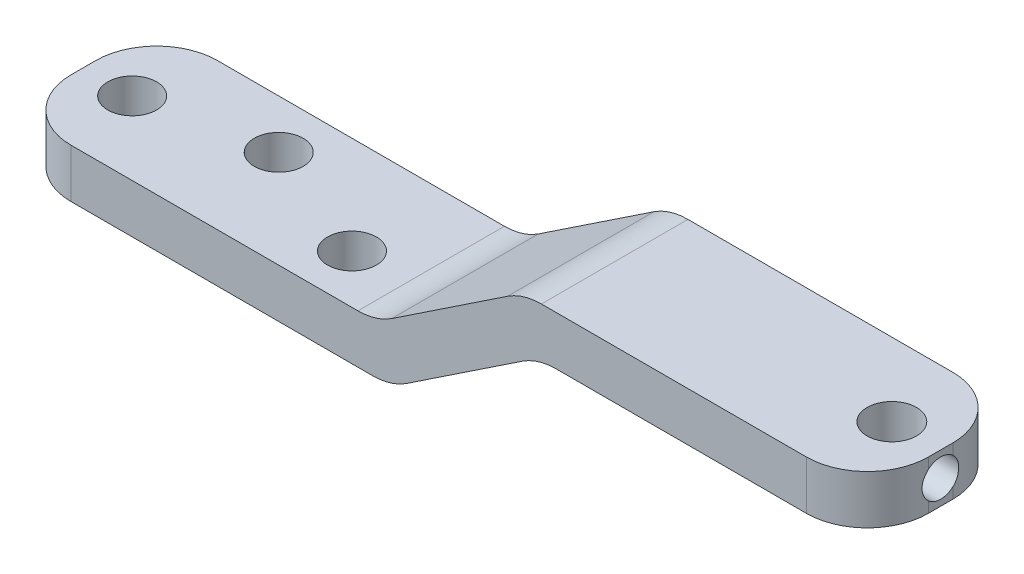
SolidWorks part; units mm, degrees
ref_plane "Front Plane" through (0, 0, 0) normal (0, 0, 1) x (1, 0, 0)
ref_plane "Top Plane" through (0, 0, 0) normal (0, 1, 0) x (1, 0, 0)
ref_plane "Right Plane" through (0, 0, 0) normal (1, 0, 0) x (0, 0, -1)
sketch "Sketch1" plane through (0, 0, 0) normal (0, 0, 1) x (1, 0, 0)
  line L0 (4, 0) -> (-23, 0)
  line L1 (-23, 0) -> (-35, -8)
  line L2 (-35, -8) -> (-66.2111, -8)
  line L3 (-66.2111, -8) -> (-66.2111, -4)
  line L4 (-66.2111, -4) -> (-36.2111, -4)
  line L5 (-36.2111, -4) -> (-24.2111, 4)
  line L6 (-24.2111, 4) -> (4, 4)
  line L7 (4, 4) -> (4, 0)
  line L8 (-29, -4) -> (-31.2188, -0.6718) construction
  dimension "D1" = 8
  dimension "D2" = 23
  dimension "D3" = 12
  dimension "D4" = 30
  dimension "D5" = 4
  dimension "D6" = 4
extrude "Boss-Extrude1" add sketch "Sketch1" along normal mid plane 12
sketch "Sketch2" plane through (0, 4, 0) normal (0, 1, 0) x (1, 0, 0)
  circle A0 centre (0, 0) radius 2.025
  dimension "D1" = 4.05
extrude "Cut-Extrude1" cut sketch "Sketch2" against normal through all
sketch "Sketch3" plane through (0, -4, 0) normal (0, 1, 0) x (1, 0, 0)
  line L0 (-66.2111, 0) -> (-42.5105, 0) construction
  line L1 (-66.2111, -6) -> (-66.2111, 6) construction
  line L2 (-36.2111, 6) -> (-66.2111, 6) construction
  line L3 (-36.2111, -6) -> (-66.2111, -6) construction
  circle A0 centre (-62.2111, 0) radius 2
  circle A1 centre (-52.2111, 2) radius 2
  circle A2 centre (-42.2111, -2) radius 2
  dimension "D1" = 4
  dimension "D2" = 4
  dimension "D3" = 4
  dimension "D4" = 4
  dimension "D5" = 10
  dimension "D6" = 10
extrude "Cut-Extrude2" cut sketch "Sketch3" against normal through all
fillet "Fillet1" radius 5 8 edges at (-23, 0, 0) (-35, -8, 0) (-36.2111, -4, 0) (-24.2111, 4, 0) (-66.2111, -6, -6) (-66.2111, -6, 6) (4, 2, -6) (4, 2, 6)
hole_wizard "M3x0.5 Tapped Hole1" positions "Sketch6" profile "Sketch5" tap size "M3x0.5" standard "Ansi Metric"
sketch "Sketch6" plane through (4, 0, 0) normal (1, 0, 0) x (0, 0, -1)
  line L0 (-1, 4) -> (1, 0) construction
  point P0 (0, 2)
sketch "Sketch5" plane through (4, 2, 0) normal (0, 1, 0) x (0, 0, -1)
  line L0 (0, 0) -> (0, 1.975)
  line L1 (0, 1.975) -> (1.5, 1.975)
  line L2 (1.5, 1.975) -> (1.5, 0)
  line L5 (1.5, 0) -> (0, 0)
  line L11 (0, -6.35) -> (0, 107.95) construction
  dimension "Thread Major Dia." = 3
  dimension "Thru Tap Drill Depth" = 1.975
